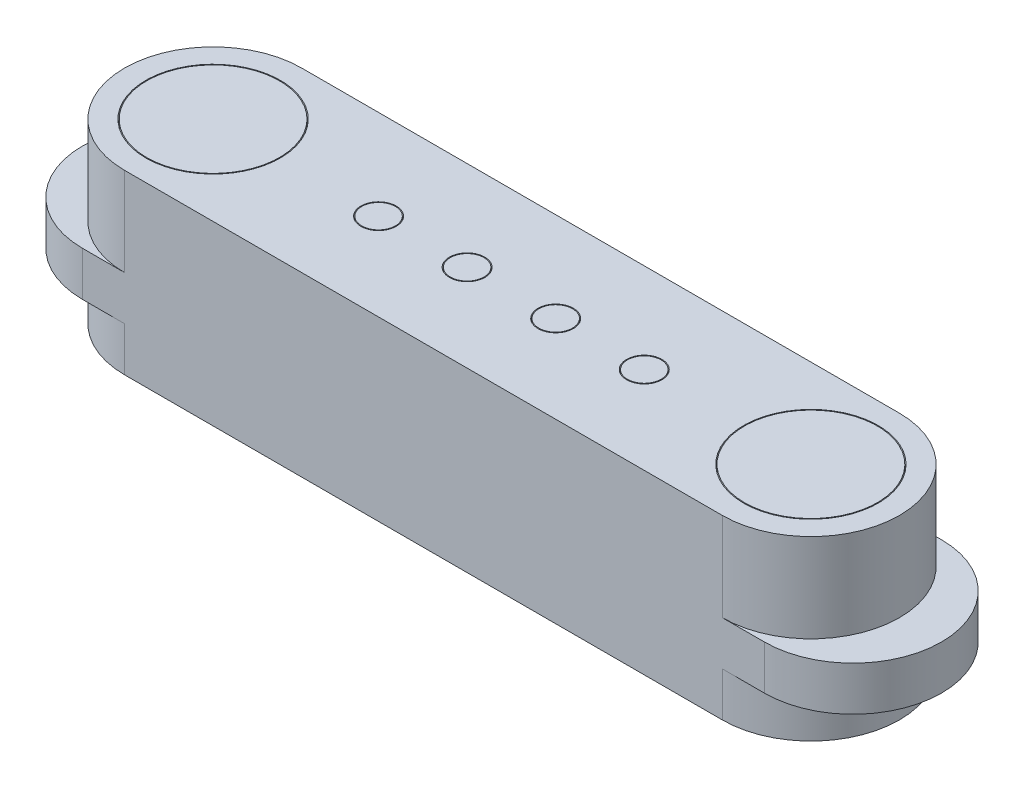
SolidWorks part; units mm, degrees
ref_plane "Front Plane" through (0, 0, 0) normal (0, 0, 1) x (1, 0, 0)
ref_plane "Top Plane" through (0, 0, 0) normal (0, 1, 0) x (1, 0, 0)
ref_plane "Right Plane" through (0, 0, 0) normal (1, 0, 0) x (0, 0, -1)
sketch "Sketch1" plane through (0, 0, 0) normal (0, 1, 0) x (1, 0, 0)
  line L0 (-3.375, 0) -> (3.375, 0) construction
  line L2 (-3.375, 1) -> (3.375, 1)
  line L3 (-3.375, -1) -> (3.375, -1)
  arc A0 (-3.375, 1) -> (-3.375, -1) centre (-3.375, 0) ccw
  arc A1 (3.375, -1) -> (3.375, 1) centre (3.375, 0) ccw
  point P5 (0, 0)
extrude "Boss-Extrude1" add sketch "Sketch1" along normal blind 2
sketch "Sketch2" plane through (0, 2, 0) normal (0, 1, 0) x (1, 0, 0)
  line L0 (-3.85, 0) -> (3.85, 0) construction
  line L2 (-3.85, 1) -> (3.85, 1)
  line L3 (-3.85, -1) -> (3.85, -1)
  arc A0 (-3.85, 1) -> (-3.85, -1) centre (-3.85, 0) ccw
  arc A1 (3.85, -1) -> (3.85, 1) centre (3.85, 0) ccw
  point P5 (0, 0)
extrude "Boss-Extrude2" add sketch "Sketch2" against normal blind 0.5 from offset 1 offset against normal yes
sketch "Sketch3" plane through (0, 2, 0) normal (0, 1, 0) x (1, 0, 0)
  line L0 (-3.375, 1) -> (-3.375, -1) construction
  line L1 (3.375, 1) -> (3.375, -1) construction
  line L2 (-3.375, 0) -> (3.375, 0) construction
  circle A0 centre (3.375, 0) radius 0.75
  circle A1 centre (-3.375, 0) radius 0.75
  circle A2 centre (-1.4922, -0.0144) radius 0.1897
  circle A3 centre (-3.375, 0) radius 0.76
  circle A4 centre (-0.4922, -0.0144) radius 0.1897
  circle A5 centre (0.5078, -0.0144) radius 0.1897
  circle A6 centre (1.5078, -0.0144) radius 0.1897
  circle A7 centre (-1.4922, -0.0144) radius 0.1997
  circle A8 centre (-0.4922, -0.0144) radius 0.1997
  circle A9 centre (0.5078, -0.0144) radius 0.1997
  circle A10 centre (1.5078, -0.0144) radius 0.1997
  circle A11 centre (3.375, 0) radius 0.76
  dimension "D1" = 1.5
  dimension "D2" = 4
  dimension "D3" = 0.01
extrude "Cut-Extrude1" cut sketch "Sketch3" against normal blind 0.1
scale "Scale1" bodies to scale 103 scale about centroid uniform scaling yes scale factor 2
